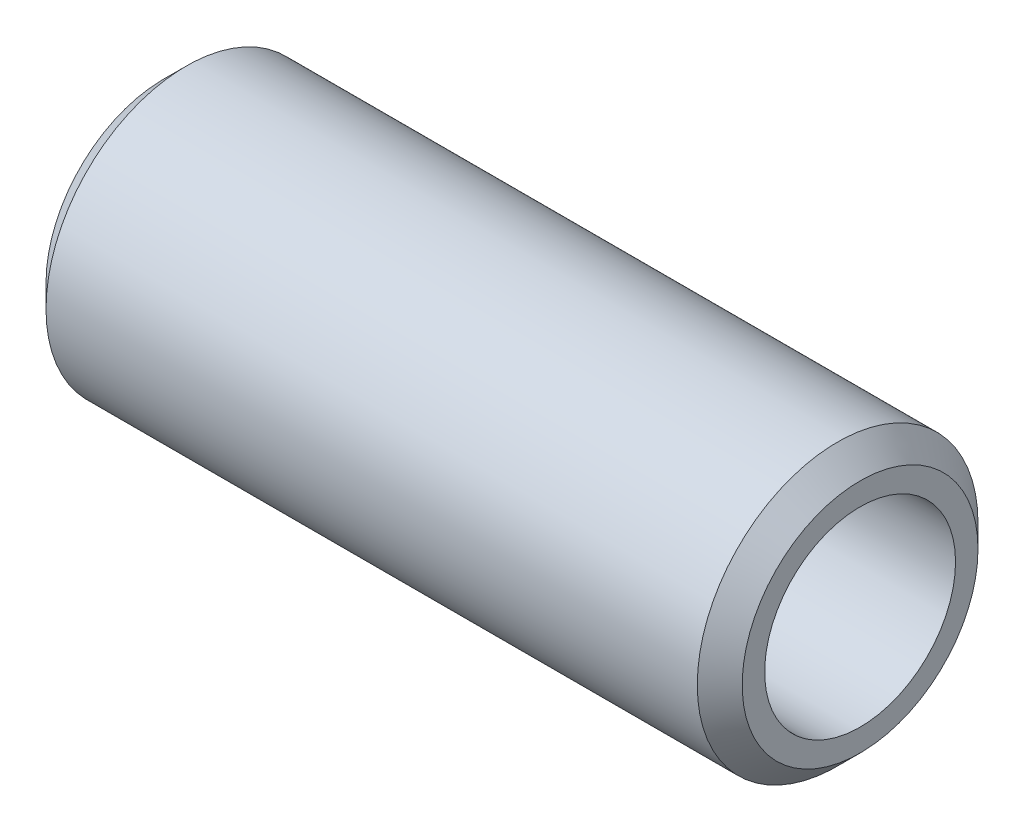
SolidWorks part; units mm, degrees
ref_plane "Front Plane" through (0, 0, 0) normal (0, 0, 1) x (1, 0, 0)
ref_plane "Top Plane" through (0, 0, 0) normal (0, 1, 0) x (1, 0, 0)
ref_plane "Right Plane" through (0, 0, 0) normal (1, 0, 0) x (0, 0, -1)
sketch "Sketch1" plane through (0, 0, 0) normal (0, 0, 1) x (1, 0, 0)
  line L0 (31, 0) -> (-31, 0) construction
  line L1 (-31, 0) -> (-31, 12.5)
  line L2 (-31, 12.5) -> (31, 12.5)
  line L3 (31, 12.5) -> (31, 0)
  line L4 (-31, 0) -> (31, 0)
  point P4 (0, 0)
  dimension "D1" = 62
  dimension "D2" = 25
revolve "Revolve1" add sketch "Sketch1" angle 360 about L0
sketch "Sketch2" plane through (31, 0, 0) normal (1, 0, 0) x (0, 0, -1)
  circle A2 centre (0, 0) radius 8.5
  circle A3 centre (0, 0) radius 8.5
  dimension "D1" = 4
extrude "Cut-Extrude1" cut sketch "Sketch2" against normal through all
chamfer "Chamfer2" distance 2 angle 45 2 edges at (31, 0, -12.5) (-31, 0, -12.5)
